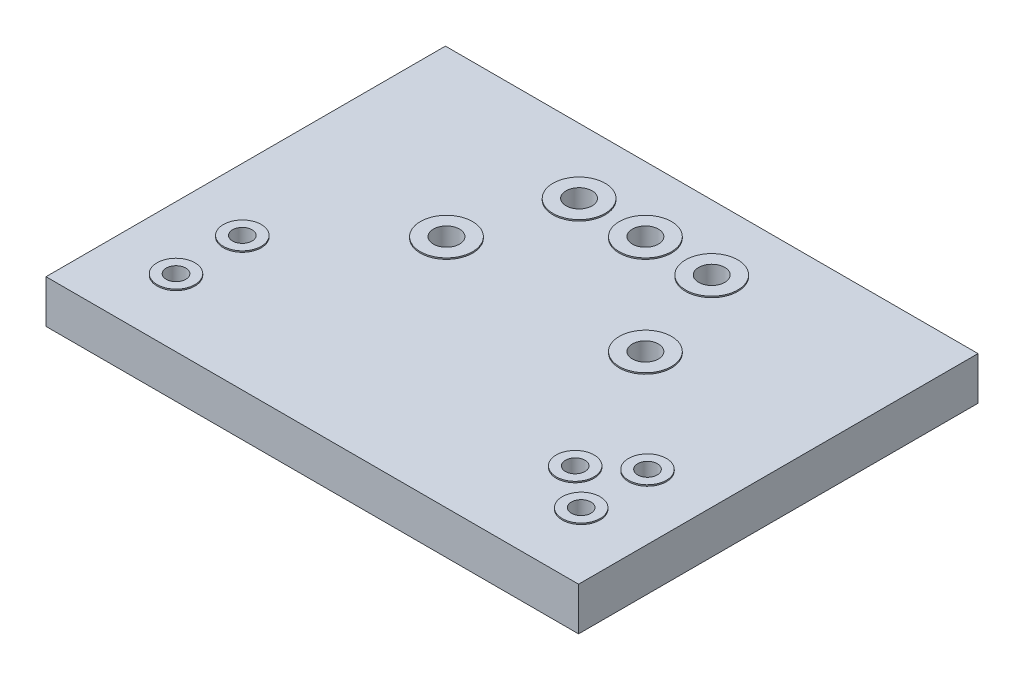
SolidWorks part; units mm, degrees
ref_plane "Front Plane" through (0, 0, 0) normal (0, 0, 1) x (1, 0, 0)
ref_plane "Top Plane" through (0, 0, 0) normal (0, 1, 0) x (1, 0, 0)
ref_plane "Right Plane" through (0, 0, 0) normal (1, 0, 0) x (0, 0, -1)
sketch "Sketch3" plane through (0, 0, 0) normal (0, 1, 0) x (1, 0, 0)
  line L0 (7.76, -2.57) -> (7.76, -5.11) construction
  line L1 (-10.2, 7.65) -> (10.2, 7.65)
  line L2 (-10.2, 7.65) -> (-10.2, -7.65)
  line L3 (-10.2, -7.65) -> (10.2, -7.65)
  line L4 (10.2, 7.65) -> (10.2, -7.65)
  line L5 (-10.2, 7.65) -> (10.2, -7.65) construction
  line L6 (-10.2, -7.65) -> (10.2, 7.65) construction
  line L7 (6.26, -3.84) -> (7.76, -3.84) construction
  line L8 (-7.76, -2.57) -> (-7.76, -5.11) construction
  line L9 (-7.76, -3.84) -> (7.76, -3.84) construction
  line L10 (-2.54, 5.11) -> (2.54, 5.11) construction
  line L11 (-3.81, 1.3) -> (3.81, 1.3) construction
  circle A0 centre (-2.54, 5.11) radius 0.5
  circle A1 centre (0, 5.11) radius 0.5
  circle A2 centre (2.54, 5.11) radius 0.5
  circle A3 centre (-7.76, -2.57) radius 0.375
  circle A4 centre (-7.76, -5.11) radius 0.375
  circle A5 centre (7.76, -2.57) radius 0.375
  circle A6 centre (7.76, -5.11) radius 0.375
  circle A7 centre (6.26, -3.84) radius 0.375
  circle A8 centre (-3.81, 1.3) radius 0.5
  circle A9 centre (3.81, 1.3) radius 0.5
  point P0 (0, 0)
  point P24 (0, -3.84)
  point P28 (0, 1.3)
  dimension "D5" = 0.75
  dimension "D7" = 1
  dimension "D1" = 15.3
  dimension "D2" = 20.4
  dimension "D3" = 1.5
  dimension "D4" = 2.54
  dimension "D6" = 15.52
  dimension "D8" = 2.54
  dimension "D9" = 2.54
  dimension "D10" = 2.54
  dimension "D11" = 7.62
  dimension "D12" = 3.81
extrude "Boss-Extrude2" add sketch "Sketch3" along normal mid plane 1.65
sketch "Sketch5" plane through (0, 0.825, 0) normal (0, 1, 0) x (1, 0, 0)
  circle A4 centre (7.76, -5.11) radius 0.375 construction
  circle A5 centre (6.26, -3.84) radius 0.375 construction
  circle A6 centre (7.76, -2.57) radius 0.375 construction
  circle A7 centre (-7.76, -5.11) radius 0.375 construction
  circle A8 centre (-7.76, -2.57) radius 0.375 construction
  circle A9 centre (-3.81, 1.3) radius 0.5 construction
  circle A10 centre (3.81, 1.3) radius 0.5 construction
  circle A11 centre (2.54, 5.11) radius 0.5 construction
  circle A12 centre (0, 5.11) radius 0.5 construction
  circle A13 centre (-2.54, 5.11) radius 0.5 construction
  circle A14 centre (7.76, -5.11) radius 0.375
  circle A15 centre (6.26, -3.84) radius 0.375
  circle A16 centre (7.76, -2.57) radius 0.375
  circle A17 centre (-7.76, -5.11) radius 0.375
  circle A18 centre (-7.76, -2.57) radius 0.375
  circle A19 centre (-3.81, 1.3) radius 0.5
  circle A20 centre (3.81, 1.3) radius 0.5
  circle A21 centre (2.54, 5.11) radius 0.5
  circle A22 centre (0, 5.11) radius 0.5
  circle A23 centre (-2.54, 5.11) radius 0.5
  circle A24 centre (-2.54, 5.11) radius 1
  circle A25 centre (0, 5.11) radius 1
  circle A26 centre (2.54, 5.11) radius 1
  circle A27 centre (3.81, 1.3) radius 1
  circle A28 centre (-3.81, 1.3) radius 1
  circle A29 centre (-7.76, -2.57) radius 0.725
  circle A30 centre (-7.76, -5.11) radius 0.725
  circle A31 centre (6.26, -3.84) radius 0.725
  circle A32 centre (7.76, -5.11) radius 0.725
  circle A33 centre (7.76, -2.57) radius 0.725
  dimension "D1" = 0.35
  dimension "D2" = 0.5
extrude "Boss-Extrude3" add sketch "Sketch5" along normal blind 0.05
mirror "Mirror1" about plane through (0, 0, 0) normal (0, 1, 0) of "Boss-Extrude3"
ref_point "Point1"
ref_plane "Plane2" through (0, 0, 5.11) normal (0, 0, 1) x (1, 0, 0)
sketch "Sketch6" plane through (0, -0.875, 0) normal (0, -1, 0) x (-1, 0, 0)
  point P0 (7.76, -2.57)
  point P1 (7.76, -5.11)
  point P3 (-7.76, -2.57)
  point P5 (-6.26, -3.84)
  point P7 (-7.76, -5.11)
